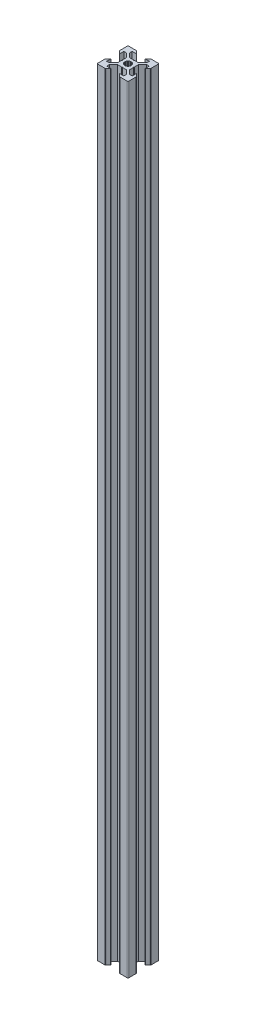
SolidWorks part; units mm, degrees
ref_plane "Alzado" through (0, 0, 0) normal (0, 0, 1) x (1, 0, 0)
ref_plane "Planta" through (0, 0, 0) normal (0, 1, 0) x (1, 0, 0)
ref_plane "Vista lateral" through (0, 0, 0) normal (1, 0, 0) x (0, 0, -1)
sketch "Croquis1" plane through (0, 0, 0) normal (0, 1, 0) x (1, 0, 0)
  line L0 (827.4237, 71.0146) -> (827.4198, 71.0542)
  line L1 (832.9566, 76.137) -> (832.9243, 76.1601)
  line L2 (827.4301, 70.9754) -> (827.4237, 71.0146)
  line L3 (832.9243, 76.1601) -> (832.8906, 76.1811)
  line L4 (827.4198, 71.0542) -> (827.4185, 71.1624)
  line L5 (827.4392, 70.9368) -> (827.4301, 70.9754)
  line L6 (827.4185, 74.7624) -> (827.4185, 71.1624)
  line L7 (827.4507, 70.8987) -> (827.4392, 70.9368)
  line L8 (827.4647, 70.8616) -> (827.4507, 70.8987)
  line L9 (827.4811, 70.8254) -> (827.4647, 70.8616)
  line L10 (827.4998, 70.7903) -> (827.4811, 70.8254)
  line L11 (842.1315, 76.2508) -> (842.1707, 76.2572)
  line L12 (832.8193, 76.2162) -> (832.7822, 76.2302)
  line L13 (827.5208, 70.7566) -> (827.4998, 70.7903)
  line L14 (832.8555, 76.1998) -> (832.8193, 76.2162)
  line L15 (827.5439, 70.7243) -> (827.5208, 70.7566)
  line L16 (827.4185, 57.7624) -> (827.4185, 61.3624)
  line L17 (827.4198, 61.4707) -> (827.4185, 61.3624)
  line L18 (827.4301, 61.5494) -> (827.4237, 61.5102)
  line L19 (827.4237, 61.5102) -> (827.4198, 61.4707)
  line L20 (827.4392, 61.5881) -> (827.4301, 61.5494)
  line L21 (827.4507, 61.6261) -> (827.4392, 61.5881)
  line L22 (827.4647, 61.6633) -> (827.4507, 61.6261)
  line L23 (827.4811, 61.6995) -> (827.4647, 61.6633)
  line L24 (827.4998, 61.7345) -> (827.4811, 61.6995)
  line L25 (827.5439, 61.8005) -> (827.5208, 61.7682)
  line L26 (827.5208, 61.7682) -> (827.4998, 61.7345)
  line L27 (832.8906, 76.1811) -> (832.8555, 76.1998)
  line L28 (827.5691, 61.8312) -> (827.5439, 61.8005)
  line L29 (827.5963, 61.8602) -> (827.5691, 61.8312)
  line L30 (827.5963, 61.8602) -> (829.1119, 63.3758)
  line L31 (829.1119, 63.3758) -> (829.2185, 63.3758)
  line L32 (829.2185, 63.3758) -> (829.2185, 60.7624)
  line L33 (829.2185, 60.7624) -> (830.8578, 60.7624)
  line L34 (830.8578, 60.7624) -> (833.5185, 63.4231)
  line L35 (827.5691, 70.6936) -> (827.5439, 70.7243)
  line L36 (833.5185, 66.0626) -> (833.5185, 63.4231)
  line L37 (833.7184, 66.2624) -> (833.5185, 66.0626)
  line L38 (833.7184, 66.2624) -> (833.5185, 66.4623)
  line L39 (833.5185, 69.1018) -> (833.5185, 66.4623)
  line L40 (830.8578, 71.7624) -> (833.5185, 69.1018)
  line L41 (829.2185, 71.7624) -> (830.8578, 71.7624)
  line L42 (829.2185, 69.149) -> (829.2185, 71.7624)
  line L43 (827.5963, 70.6646) -> (827.5691, 70.6936)
  line L44 (829.1119, 69.149) -> (829.2185, 69.149)
  line L45 (829.1119, 69.149) -> (827.5963, 70.6646)
  line L46 (845.6185, 60.7624) -> (843.9791, 60.7624)
  line L47 (832.7822, 76.2302) -> (832.7442, 76.2417)
  line L48 (832.9873, 76.1118) -> (832.9566, 76.137)
  line L49 (833.0163, 76.0846) -> (832.9873, 76.1118)
  line L50 (832.7442, 76.2417) -> (832.7055, 76.2508)
  line L51 (832.6267, 56.2637) -> (832.587, 56.2624)
  line L52 (832.6663, 56.2676) -> (832.6267, 56.2637)
  line L53 (832.7055, 56.2741) -> (832.6663, 56.2676)
  line L54 (832.7442, 56.2831) -> (832.7055, 56.2741)
  line L55 (832.7822, 56.2946) -> (832.7442, 56.2831)
  line L56 (832.8193, 56.3086) -> (832.7822, 56.2946)
  line L57 (831.9185, 72.8231) -> (834.5791, 70.1624)
  line L58 (832.8555, 56.325) -> (832.8193, 56.3086)
  line L59 (832.8906, 56.3438) -> (832.8555, 56.325)
  line L60 (832.9243, 56.3647) -> (832.8906, 56.3438)
  line L61 (832.9566, 56.3879) -> (832.9243, 56.3647)
  line L62 (832.9873, 56.4131) -> (832.9566, 56.3879)
  line L63 (833.0163, 56.4402) -> (832.9873, 56.4131)
  line L64 (833.0163, 56.4402) -> (834.5319, 57.9558)
  line L65 (834.5319, 57.9558) -> (834.5319, 58.0624)
  line L66 (834.5319, 58.0624) -> (831.9185, 58.0624)
  line L67 (831.9185, 58.0624) -> (831.9185, 59.7018)
  line L68 (831.9185, 59.7018) -> (834.5791, 62.3624)
  line L69 (834.5791, 62.3624) -> (837.2115, 62.3624)
  line L70 (837.2115, 62.3624) -> (837.4185, 62.5672)
  line L71 (837.4185, 62.5672) -> (837.6233, 62.3624)
  line L72 (837.6233, 62.3624) -> (840.2578, 62.3624)
  line L73 (840.2578, 62.3624) -> (842.9185, 59.7018)
  line L74 (842.9185, 58.0624) -> (842.9185, 59.7018)
  line L75 (833.0163, 76.0846) -> (834.5319, 74.569)
  line L76 (840.3051, 58.0624) -> (842.9185, 58.0624)
  line L77 (832.7055, 76.2508) -> (832.6663, 76.2572)
  line L78 (840.3051, 57.9558) -> (840.3051, 58.0624)
  line L79 (840.3051, 57.9558) -> (841.8207, 56.4402)
  line L80 (841.8207, 56.4402) -> (841.8497, 56.4131)
  line L81 (841.8497, 56.4131) -> (841.8804, 56.3879)
  line L82 (841.8804, 56.3879) -> (841.9127, 56.3647)
  line L83 (841.9127, 56.3647) -> (841.9464, 56.3438)
  line L84 (841.9464, 56.3438) -> (841.9814, 56.325)
  line L85 (841.9814, 56.325) -> (842.0176, 56.3086)
  line L86 (842.0176, 56.3086) -> (842.0548, 56.2946)
  line L87 (842.0548, 56.2946) -> (842.0928, 56.2831)
  line L88 (842.0928, 56.2831) -> (842.1315, 56.2741)
  line L89 (842.1315, 56.2741) -> (842.1707, 56.2676)
  line L90 (842.1707, 56.2676) -> (842.2102, 56.2637)
  line L91 (842.2102, 56.2637) -> (842.2499, 56.2624)
  line L92 (845.9185, 56.2624) -> (842.2499, 56.2624)
  line L93 (834.5319, 74.569) -> (834.5319, 74.4624)
  line L94 (832.6663, 76.2572) -> (832.6267, 76.2611)
  line L95 (847.4185, 57.7624) -> (847.4185, 61.431)
  line L96 (847.4172, 61.4707) -> (847.4185, 61.431)
  line L97 (847.4133, 61.5102) -> (847.4172, 61.4707)
  line L98 (847.4068, 61.5494) -> (847.4133, 61.5102)
  line L99 (847.3978, 61.5881) -> (847.4068, 61.5494)
  line L100 (847.3863, 61.6261) -> (847.3978, 61.5881)
  line L101 (847.3723, 61.6633) -> (847.3863, 61.6261)
  line L102 (847.3559, 61.6995) -> (847.3723, 61.6633)
  line L103 (832.6267, 76.2611) -> (832.587, 76.2624)
  line L104 (847.3372, 61.7345) -> (847.3559, 61.6995)
  line L105 (847.3162, 61.7682) -> (847.3372, 61.7345)
  line L106 (847.293, 61.8005) -> (847.3162, 61.7682)
  line L107 (847.2678, 61.8312) -> (847.293, 61.8005)
  line L108 (847.2407, 61.8602) -> (847.2678, 61.8312)
  line L109 (845.7251, 63.3758) -> (847.2407, 61.8602)
  line L110 (845.7251, 63.3758) -> (845.6185, 63.3758)
  line L111 (845.6185, 63.3758) -> (845.6185, 60.7624)
  line L112 (842.0548, 76.2302) -> (842.0928, 76.2417)
  line L113 (843.9791, 60.7624) -> (841.3185, 63.4231)
  line L114 (841.3185, 63.4231) -> (841.3185, 66.0626)
  line L115 (841.1186, 66.2624) -> (841.3185, 66.0626)
  line L116 (841.1186, 66.2624) -> (841.3185, 66.4623)
  line L117 (841.3185, 69.1018) -> (841.3185, 66.4623)
  line L118 (843.9791, 71.7624) -> (841.3185, 69.1018)
  line L119 (828.9185, 76.2624) -> (832.587, 76.2624)
  line L120 (845.7251, 69.149) -> (845.6185, 69.149)
  line L121 (845.6185, 71.7624) -> (843.9791, 71.7624)
  line L122 (845.6185, 69.149) -> (845.6185, 71.7624)
  line L123 (847.2407, 70.6646) -> (845.7251, 69.149)
  line L124 (847.2407, 70.6646) -> (847.2678, 70.6936)
  line L125 (847.2678, 70.6936) -> (847.293, 70.7243)
  line L126 (847.293, 70.7243) -> (847.3162, 70.7566)
  line L127 (847.3162, 70.7566) -> (847.3372, 70.7903)
  line L128 (847.3372, 70.7903) -> (847.3559, 70.8254)
  line L129 (847.3559, 70.8254) -> (847.3723, 70.8616)
  line L130 (847.3723, 70.8616) -> (847.3863, 70.8987)
  line L131 (847.3863, 70.8987) -> (847.3978, 70.9368)
  line L132 (847.3978, 70.9368) -> (847.4068, 70.9754)
  line L133 (847.4068, 70.9754) -> (847.4133, 71.0146)
  line L134 (847.4133, 71.0146) -> (847.4172, 71.0542)
  line L135 (847.4172, 71.0542) -> (847.4185, 71.0939)
  line L136 (834.5319, 74.4624) -> (831.9185, 74.4624)
  line L137 (845.9185, 76.2624) -> (842.2499, 76.2624)
  line L138 (842.2102, 76.2611) -> (842.2499, 76.2624)
  line L139 (842.1707, 76.2572) -> (842.2102, 76.2611)
  line L140 (842.0928, 76.2417) -> (842.1315, 76.2508)
  line L141 (842.0176, 76.2162) -> (842.0548, 76.2302)
  line L142 (841.9814, 76.1998) -> (842.0176, 76.2162)
  line L143 (841.9464, 76.1811) -> (841.9814, 76.1998)
  line L144 (841.9127, 76.1601) -> (841.9464, 76.1811)
  line L145 (841.8804, 76.137) -> (841.9127, 76.1601)
  line L146 (841.8497, 76.1118) -> (841.8804, 76.137)
  line L147 (841.8207, 76.0846) -> (841.8497, 76.1118)
  line L148 (840.3051, 74.569) -> (841.8207, 76.0846)
  line L149 (840.3051, 74.569) -> (840.3051, 74.4624)
  line L150 (840.3051, 74.4624) -> (842.9185, 74.4624)
  line L151 (842.9185, 74.4624) -> (842.9185, 72.8231)
  line L152 (840.2578, 70.1624) -> (842.9185, 72.8231)
  line L153 (840.2578, 70.1624) -> (837.6233, 70.1624)
  line L154 (831.9185, 74.4624) -> (831.9185, 72.8231)
  line L155 (837.6233, 70.1624) -> (837.4185, 69.9577)
  line L156 (837.2137, 70.1624) -> (837.4185, 69.9577)
  line L157 (834.5791, 70.1624) -> (837.2137, 70.1624)
  line L158 (835.5998, 65.2124) -> (835.9336, 64.7775)
  line L159 (835.39, 65.7189) -> (835.5998, 65.2124)
  line L160 (835.3185, 66.2624) -> (835.39, 65.7189)
  line L161 (835.39, 66.8059) -> (835.3185, 66.2624)
  line L162 (835.5998, 67.3124) -> (835.39, 66.8059)
  line L163 (835.9336, 67.7473) -> (835.5998, 67.3124)
  line L164 (836.3685, 68.0811) -> (835.9336, 67.7473)
  line L165 (836.875, 68.2909) -> (836.3685, 68.0811)
  line L166 (837.4185, 68.3624) -> (836.875, 68.2909)
  line L167 (837.962, 68.2909) -> (837.4185, 68.3624)
  line L168 (838.4685, 68.0811) -> (837.962, 68.2909)
  line L169 (838.9034, 67.7473) -> (838.4685, 68.0811)
  line L170 (839.2371, 67.3124) -> (838.9034, 67.7473)
  line L171 (839.4469, 66.8059) -> (839.2371, 67.3124)
  line L172 (839.5185, 66.2624) -> (839.4469, 66.8059)
  line L173 (839.4469, 65.7189) -> (839.5185, 66.2624)
  line L174 (839.2371, 65.2124) -> (839.4469, 65.7189)
  line L175 (838.9034, 64.7775) -> (839.2371, 65.2124)
  line L176 (838.4685, 64.4438) -> (838.9034, 64.7775)
  line L177 (837.962, 64.234) -> (838.4685, 64.4438)
  line L178 (837.4185, 64.1624) -> (837.962, 64.234)
  line L179 (836.875, 64.234) -> (837.4185, 64.1624)
  line L180 (836.3685, 64.4438) -> (836.875, 64.234)
  line L181 (835.9336, 64.7775) -> (836.3685, 64.4438)
  line L182 (828.9185, 76.2624) -> (827.9185, 76.2624)
  line L183 (827.4185, 74.7624) -> (827.4185, 75.7624)
  line L184 (845.9185, 76.2624) -> (846.9185, 76.2624)
  line L185 (847.4185, 57.7624) -> (847.4185, 56.7624)
  line L186 (845.9185, 56.2624) -> (846.9185, 56.2624)
  line L187 (847.4185, 71.0939) -> (847.4185, 75.7624)
  line L188 (827.9185, 56.2624) -> (832.587, 56.2624)
  line L189 (827.4185, 57.7624) -> (827.4185, 56.7624)
  arc A0 (827.4185, 56.7624) -> (827.9185, 56.2624) centre (827.9185, 56.7624) ccw
  arc A2 (827.9185, 76.2624) -> (827.4185, 75.7624) centre (827.9185, 75.7624) ccw
  arc A3 (847.4185, 75.7624) -> (846.9185, 76.2624) centre (846.9185, 75.7624) ccw
  arc A4 (846.9185, 56.2624) -> (847.4185, 56.7624) centre (846.9185, 56.7624) ccw
extrude "Saliente-Extruir1" add sketch "Croquis1" along normal blind 500
